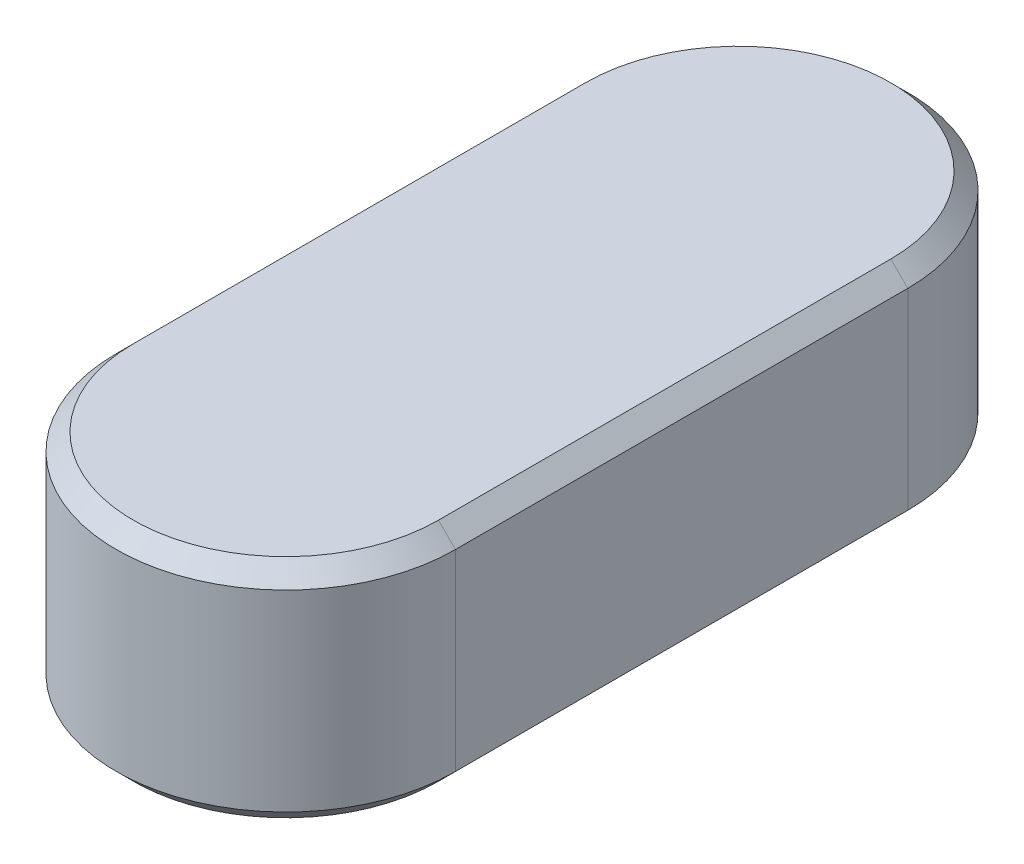
SolidWorks part; units mm, degrees
material "AISI 4340 Steel, normalized"
ref_plane "Front Plane" through (0, 0, 0) normal (0, 0, 1) x (1, 0, 0)
ref_plane "Top Plane" through (0, 0, 0) normal (0, 1, 0) x (1, 0, 0)
ref_plane "Right Plane" through (0, 0, 0) normal (1, 0, 0) x (0, 0, -1)
sketch "Sketch1" plane through (0, 0, 0) normal (0, 1, 0) x (1, 0, 0)
  line L0 (0, 0) -> (0, 16) construction
  line L1 (6, 0) -> (6, 16)
  line L2 (-6, 0) -> (-6, 16)
  arc A0 (6, 0) -> (-6, 0) centre (0, 0) cw
  arc A1 (6, 16) -> (-6, 16) centre (0, 16) ccw
  dimension "D1" = 16
  dimension "D2" = 6
  dimension "D3" = 6
extrude "Boss-Extrude1" add sketch "Sketch1" along normal blind 8
chamfer "Chamfer1" distance 0.6 8 edges at (-6, 0, -8) (0, 0, 6) (0, 0, -22) (6, 0, -8) (-6, 8, -8) (0, 8, 6) (0, 8, -22) (6, 8, -8)
